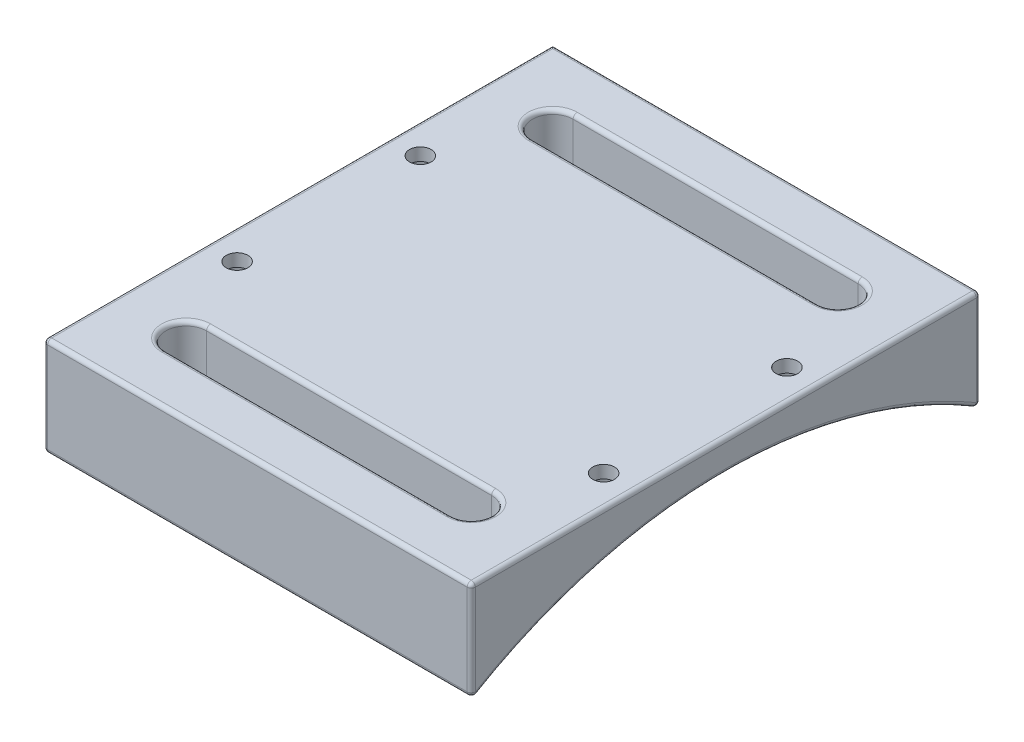
SolidWorks part; units mm, degrees
ref_plane "Front Plane" through (0, 0, 0) normal (0, 0, 1) x (1, 0, 0)
ref_plane "Top Plane" through (0, 0, 0) normal (0, 1, 0) x (1, 0, 0)
ref_plane "Right Plane" through (0, 0, 0) normal (1, 0, 0) x (0, 0, -1)
sketch "Sketch1" plane through (0, 0, 0) normal (0, 1, 0) x (1, 0, 0)
  line L1 (0, 0) -> (53.34, 0)
  line L2 (0, 0) -> (0, 63.5)
  line L3 (0, 63.5) -> (53.34, 63.5)
  line L4 (53.34, 0) -> (53.34, 63.5)
  dimension "D1" = 53.34
  dimension "D2" = 63.5
extrude "Boss-Extrude1" add sketch "Sketch1" along normal blind 12.7
sketch "Sketch3" plane through (0, 12.7, 0) normal (0, 1, 0) x (1, 0, 0)
  line L4 (53.34, 63.5) -> (0, 63.5) construction
  line L6 (53.34, 0) -> (53.34, 63.5) construction
  point P0 (3.81, 43.18)
  point P1 (49.53, 43.18)
  point P2 (3.81, 20.32)
  point P3 (49.53, 20.32)
  point P8 (0, 0)
  point P9 (0, 0)
  point P10 (0, 0)
  point P11 (0, 0)
  dimension "D1" = 45.72
  dimension "D2" = 45.72
  dimension "D3" = 22.86
  dimension "D4" = 20.32
  dimension "D5" = 3.81
sketch "Sketch9" plane through (0, 12.7, 0) normal (0, 1, 0) x (1, 0, 0)
  line L0 (0, 63.5) -> (0, 0) construction
  line L1 (8.89, 11.43) -> (44.45, 11.43)
  line L3 (8.89, 6.35) -> (44.45, 6.35)
  line L5 (0, 0) -> (53.34, 0) construction
  line L6 (0, 31.75) -> (4.9341, 31.75) construction
  line L9 (8.89, 57.15) -> (44.45, 57.15)
  line L10 (8.89, 52.07) -> (44.45, 52.07)
  arc A0 (44.45, 6.35) -> (44.45, 11.43) centre (44.45, 8.89) ccw
  arc A1 (8.89, 11.43) -> (8.89, 6.35) centre (8.89, 8.89) ccw
  arc A4 (8.89, 52.07) -> (8.89, 57.15) centre (8.89, 54.61) cw
  arc A5 (44.45, 57.15) -> (44.45, 52.07) centre (44.45, 54.61) cw
  dimension "D2" = 8.89
  dimension "D1" = 35.56
  dimension "D3" = 6.35
  dimension "D4" = 5.08
extrude "Cut-Extrude2" cut sketch "Sketch9" against normal blind 67.818
sketch "Sketch11" plane through (53.34, 0, 0) normal (1, 0, 0) x (0, 0, -1)
  line L0 (31.75, 0) -> (31.75, -5.023) construction
  line L1 (0, 0) -> (63.5, 0) construction
  line L2 (0, 0) -> (63.5, 0)
  arc A0 (0, 0) -> (63.5, 0) centre (31.75, -52.2514) cw
  point P9 (31.75, 8.89)
  dimension "D1" = 8.89
extrude "Cut-Extrude3" cut sketch "Sketch11" against normal through all
ref_plane "Plane2" through (0, 7.62, 0) normal (0, 1, 0) x (1, 0, 0)
sketch "Sketch16" plane through (0, 7.62, 0) normal (0, 1, 0) x (1, 0, 0)
  point P0 (49.53, 43.18)
  point P2 (3.81, 43.18)
  point P4 (3.81, 20.32)
  point P6 (49.53, 20.32)
hole_wizard "CBORE for M2.5 SHCS3" positions "Sketch19" profile "Sketch20" counterbore size "M2.5" standard "ANSI Metric"
sketch "Sketch19" plane through (0, 7.62, 0) normal (0, 1, 0) x (1, 0, 0)
  point P0 (49.53, 20.32)
  point P3 (49.53, 43.18)
  point P6 (3.81, 43.18)
  point P9 (3.81, 20.32)
sketch "Sketch20" plane through (49.53, 7.62, -20.32) normal (1, 0, 0) x (0, 0, -1)
  line L0 (0, 0) -> (0, 5.08)
  line L1 (0, 5.08) -> (1.35, 5.08)
  line L3 (1.35, 5.08) -> (1.35, 3.5)
  line L4 (1.35, 3.5) -> (3.25, 3.5)
  line L5 (3.25, 3.5) -> (3.25, 0)
  line L7 (3.25, 0) -> (0, 0)
  line L11 (0, -6.35) -> (0, 107.95) construction
  dimension "Thru Hole Dia." = 2.7
  dimension "Thru Hole Depth" = 5.08
  dimension "C'Bore Dia." = 6.5
  dimension "C'Bore Depth" = 3.5
sketch "Sketch21" plane through (0, 7.62, 0) normal (0, 1, 0) x (1, 0, 0)
  circle A0 centre (49.53, 43.18) radius 3.25
  circle A1 centre (3.81, 43.18) radius 3.25
  circle A2 centre (3.81, 20.32) radius 3.25
  circle A3 centre (49.53, 20.32) radius 3.25
extrude "Cut-Extrude4" cut sketch "Sketch21" against normal through all
fillet "Fillet1" radius 0.508 27 edges at (46.99, 12.7, -8.89) (26.67, 12.7, -6.35) (6.35, 12.7, -8.89) (6.3533, 4.5078, -9.0197) (26.67, 3.3643, -6.35) (46.9854, 4.3941, -8.7378) (46.99, 12.7, -54.61) (26.67, 12.7, -52.07) (6.35, 12.7, -54.61) (53.34, 12.7, -31.75) (53.34, 6.35, -63.5) (53.34, 6.35, 0) (6.3546, 4.3941, -54.7622) (26.67, 3.3643, -57.15) (46.9867, 4.5078, -54.4803) (26.67, 5.4146, -52.07) (26.67, 0, -63.5) (0, 8.89, -31.75) (26.67, 0, 0) (53.34, 8.89, -31.75) (26.67, 12.7, -11.43) (26.67, 5.4146, -11.43) (26.67, 12.7, -57.15) (0, 12.7, -31.75) (26.67, 12.7, -63.5) (26.67, 12.7, 0) (0, 6.35, 0)
